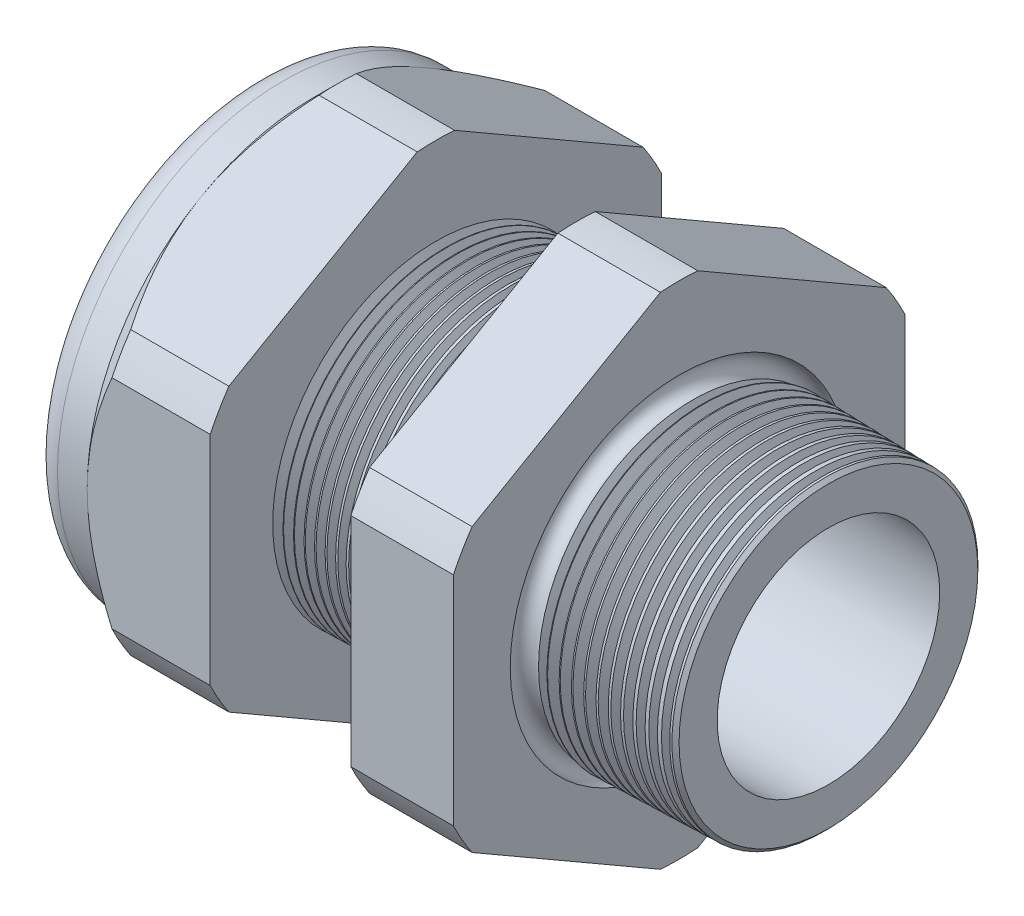
SolidWorks part; units mm, degrees
ref_plane "Front Plane" through (0, 0, 0) normal (0, 0, 1) x (1, 0, 0)
ref_plane "Top Plane" through (0, 0, 0) normal (0, 1, 0) x (1, 0, 0)
ref_plane "Right Plane" through (0, 0, 0) normal (1, 0, 0) x (0, 0, -1)
sketch "Sketch10" plane through (0, 0, 0) normal (0, 0, 1) x (1, 0, 0)
  line L0 (0, 0) -> (-115.3565, 0) construction
  line L1 (-38.862, 9.017) -> (-25.662, 9.017)
  line L2 (3.048, 8.1382) -> (3.048, 11.1862)
  line L3 (-7.874, 11.4722) -> (3.048, 11.1862)
  line L4 (-7.874, 33.02) -> (-7.874, 11.4722)
  line L5 (-7.874, 33.02) -> (-15.374, 33.02)
  line L6 (-15.374, 33.02) -> (-15.374, 11.6686)
  line L7 (-25.662, 11.938) -> (-15.374, 11.6686)
  line L8 (-25.662, 11.938) -> (-25.662, 33.02)
  line L9 (-25.662, 33.02) -> (-34.662, 33.02)
  line L10 (-34.662, 33.02) -> (-34.662, 16.51)
  line L11 (-34.662, 16.51) -> (-38.862, 16.51)
  line L12 (-38.862, 16.51) -> (-38.862, 9.017)
  line L13 (-25.662, 9.017) -> (3.048, 8.1382)
  dimension "D1" = 41.91
  dimension "D2" = 18.034
  dimension "D3" = 1.5
  dimension "D4" = 3.048
  dimension "A" = 23.876
  dimension "D6" = 33.02
  dimension "D8" = 66.04
  dimension "D9" = 4.2
  dimension "D10" = 9
  dimension "D11" = 7.5
  dimension "D" = 10.922
revolve "Revolve2" add sketch "Sketch10" angle 360 about L0
sketch "Sketch12" plane through (-34.662, 0, 0) normal (-1, 0, 0) x (0, 0, 1)
  line L1 (-1.3666, 18.2751) -> (-15.1434, 10.3211)
  line L2 (-16.51, 7.954) -> (-16.51, -7.954)
  line L3 (-15.1434, -10.3211) -> (-1.3666, -18.2751)
  line L4 (1.3666, -18.2751) -> (15.1434, -10.3211)
  line L5 (16.51, -7.954) -> (16.51, 7.954)
  line L6 (15.1434, 10.3211) -> (1.3666, 18.2751)
  circle A0 centre (0, 0) radius 16.51 construction
  arc A1 (1.3666, 18.2751) -> (-1.3666, 18.2751) centre (0, 0) ccw
  arc A2 (-15.1434, 10.3211) -> (-16.51, 7.954) centre (0, 0) ccw
  arc A3 (-16.51, -7.954) -> (-15.1434, -10.3211) centre (0, 0) ccw
  arc A4 (-1.3666, -18.2751) -> (1.3666, -18.2751) centre (0, 0) ccw
  arc A5 (15.1434, -10.3211) -> (16.51, -7.954) centre (0, 0) ccw
  arc A6 (16.51, 7.954) -> (15.1434, 10.3211) centre (0, 0) ccw
  dimension "D2" = 36.6522
  dimension "D1" = 33.02
extrude "Cut-Extrude2" cut sketch "Sketch12" against normal through all flip side to cut
fillet "Fillet4" radius 2.032 1 edges at (-38.862, 0, -16.51)
sketch "Sketch19" plane through (-34.662, 0, 0) normal (-1, 0, 0) x (0, 0, 1)
  line L0 (16.51, 0) -> (16.51, 7.954) construction
  circle A0 centre (0, 0) radius 16.51
extrude "Cut-Extrude3" cut sketch "Sketch19" against normal blind 3.998 draft 45 flip side to cut
chamfer "Chamfer1" distance 0.254 angle 45 1 edges at (3.048, 0, -11.1862)
sketch "Sketch21" plane through (-38.862, 0, 0) normal (-1, 0, 0) x (0, 0, 1)
  circle A0 centre (0, 0) radius 9.017
  circle A2 centre (0, 0) radius 9.017 construction
extrude "plug" add sketch "Sketch21" against normal blind 8.89 separate body
sketch "Sketch22" plane through (-38.862, 0, 0) normal (-1, 0, 0) x (0, 0, 1)
  circle A0 centre (0, 0) radius 8.763
  circle A1 centre (0, 0) radius 9.017 construction
  dimension "D1" = 0.254
extrude "Cut-Extrude4" cut sketch "Sketch22" against normal blind 0.508
sketch "Sketch27" plane through (-38.354, 0, 0) normal (-1, 0, 0) x (0, 0, 1)
  line L0 (-4.3624, 0) -> (4.3624, 0) construction
  circle A0 centre (-5.1928, 0) radius 3.556
  circle A1 centre (0, 0) radius 8.763 construction
  dimension "D1" = 0.0142
  dimension "holedia" = 7.112
extrude "plugholes" cut sketch "Sketch27" against normal through all
pattern_circular "CirPattern1" count 3 over 360 about axis through (0, 0, 0) along (1, 0, 0) of "plugholes"
sketch "Sketch28" [suppressed] plane through (-29.464, 0, 0) normal (-1, 0, 0) x (0, 0, 1)
  circle A0 centre (0, 0) radius 0.762
  dimension "midholedia" = 7.112
extrude "midhole" [suppressed] cut sketch "Sketch28" against normal through all
sketch "Sketch29" plane through (0, 0, 0) normal (0, 0, 1) x (1, 0, 0)
  line L0 (-25.662, 11.938) -> (-24.929, 11.9188)
  line L1 (-15.374, 11.6686) -> (-25.662, 11.938) construction
  line L2 (-24.929, 11.9188) -> (-25.3121, 11.2936)
  line L3 (-25.3121, 11.2936) -> (-25.662, 11.938)
  dimension "D1" = 60
  dimension "D2" = 60
  dimension "D3" = 0.635
revolve "Cut-Revolve1" cut sketch "Sketch29" angle 360 about axis through (0, 0, 0) along (-1, 0, 0)
pattern_linear "LPattern1" count 14 spacing 0.762 along (1, 0, 0) of "Cut-Revolve1"
sketch "Sketch30" plane through (0, 0, 0) normal (0, 0, 1) x (1, 0, 0)
  line L0 (-7.874, 11.4722) -> (-6.9944, 11.4492)
  line L1 (-7.874, 18.2751) -> (-7.874, 10.3211) construction
  line L2 (2.7941, 11.1929) -> (-7.874, 11.4722) construction
  line L3 (-6.9944, 11.4492) -> (-7.4542, 10.6989)
  line L4 (-7.4542, 10.6989) -> (-7.874, 11.4722)
  dimension "D1" = 60
  dimension "D2" = 60
  dimension "D3" = 0.762
revolve "Cut-Revolve2" cut sketch "Sketch30" angle 360 about axis through (0, 0, 0) along (-1, 0, 0)
pattern_linear "LPattern2" count 12 spacing 0.889 along (1, 0, 0) of "Cut-Revolve2"
sketch "Sketch31" [suppressed] plane through (-38.354, 0, 0) normal (-1, 0, 0) x (0, 0, 1)
  line L0 (-1.905, 1.905) -> (1.905, 1.905)
  line L1 (-1.905, -1.905) -> (1.905, -1.905)
  circle A0 centre (0, 0) radius 1.905 construction
  arc A1 (-1.905, 1.905) -> (-1.905, -1.905) centre (-1.905, 0) ccw
  arc A2 (1.905, 1.905) -> (1.905, -1.905) centre (1.905, 0) cw
extrude "Cut-Extrude5" [suppressed] cut sketch "Sketch31" against normal through all
sketch "Sketch32" plane through (0, 0, 0) normal (0, 0, 1) x (1, 0, 0)
  line L0 (-7.874, 18.2751) -> (-7.874, 10.3211) construction
  circle A0 centre (-7.747, 11.4722) radius 0.889
  dimension "D2" = 1.778
  dimension "D1" = 0.127
revolve "Cut-Revolve3" cut sketch "Sketch32" angle 360 about axis through (0, 0, 0) along (-1, 0, 0)
